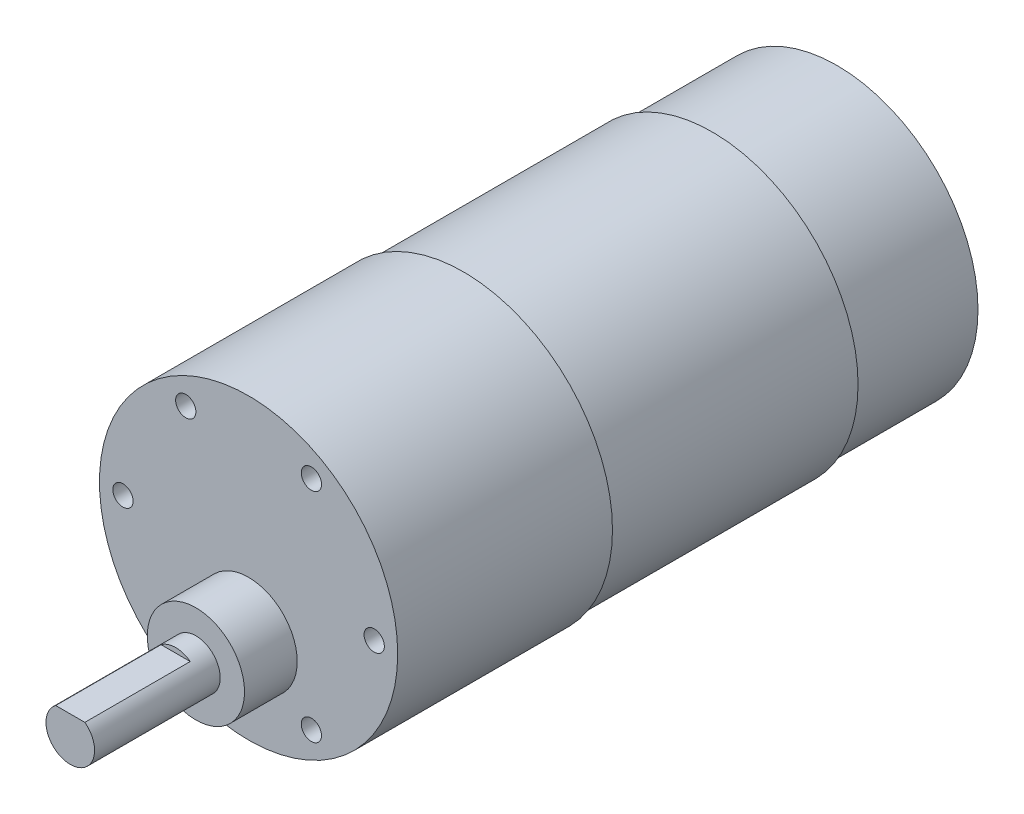
SolidWorks part; units mm, degrees
ref_plane "Front Plane" through (0, 0, 0) normal (0, 0, 1) x (1, 0, 0)
ref_plane "Top Plane" through (0, 0, 0) normal (0, 1, 0) x (1, 0, 0)
ref_plane "Right Plane" through (0, 0, 0) normal (1, 0, 0) x (0, 0, -1)
sketch "Sketch1" plane through (0, 0, 0) normal (0, 0, 1) x (1, 0, 0)
  circle A0 centre (0, 0) radius 17.4
  dimension "D1" = 34.8
extrude "Boss-Extrude1" add sketch "Sketch1" along normal blind 15.4
sketch "Sketch2" plane through (0, 0, 15.4) normal (0, 0, 1) x (1, 0, 0)
  circle A0 centre (0, 0) radius 18
  dimension "D1" = 36
extrude "Boss-Extrude2" add sketch "Sketch2" along normal blind 30.7
sketch "Sketch3" plane through (0, 0, 46.1) normal (0, 0, 1) x (1, 0, 0)
  circle A0 centre (0, 0) radius 18.4
  dimension "D1" = 36.8
extrude "Boss-Extrude3" add sketch "Sketch3" along normal blind 26.5
sketch "Sketch4" plane through (0, 0, 72.6) normal (0, 0, 1) x (1, 0, 0)
  circle A0 centre (0, -7) radius 6
  dimension "D2" = 12
  dimension "D1" = 7
extrude "Boss-Extrude4" add sketch "Sketch4" along normal blind 6.5
sketch "Sketch5" plane through (0, 0, 79.1) normal (0, 0, 1) x (1, 0, 0)
  circle A0 centre (0, -7) radius 3
  dimension "D1" = 6
extrude "Boss-Extrude5" add sketch "Sketch5" along normal blind 15.5
sketch "Sketch6" plane through (0, 0, 94.6) normal (0, 0, 1) x (1, 0, 0)
  line L0 (-1.8, -4.6) -> (1.8, -4.6)
  circle A0 centre (0, -7) radius 3 construction
  circle A1 centre (0, -7) radius 3 construction
  arc A2 (-1.8, -4.6) -> (1.8, -4.6) centre (0, -7) cw
  dimension "D1" = 2.4
extrude "Cut-Extrude1" cut sketch "Sketch6" against normal blind 13
hole_wizard "Tap Drill for M3x0.5 Tap1" positions "Sketch7" profile "Sketch8" hole size "M3x0.5" standard "ANSI Metric"
sketch "Sketch7" plane through (0, 0, 72.6) normal (0, 0, 1) x (1, 0, 0)
  circle A0 centre (0, 0) radius 15.5
  point P0 (-15.5, 0)
  point P13 (-7.75, 13.4234)
  point P14 (7.75, 13.4234)
  point P15 (15.5, 0)
  point P16 (7.75, -13.4234)
  point P17 (-7.75, -13.4234)
  dimension "D1" = 15.5
  dimension "D2" = 6
sketch "Sketch8" plane through (-15.5, 0, 72.6) normal (1, 0, 0) x (0, -1, 0)
  line L0 (0, 0) -> (0, 10.76)
  line L1 (0, 10.76) -> (1.25, 10.76)
  line L2 (1.25, 10.76) -> (1.25, 0)
  line L5 (1.25, 0) -> (0, 0)
  line L10 (0, 10.76) -> (-1.25, 10.76) construction
  line L11 (0, -6.35) -> (0, 107.95) construction
  dimension "Hole Dia." = 2.5
  dimension "Hole Depth" = 10.76
  dimension "Drill Angle" = 180
